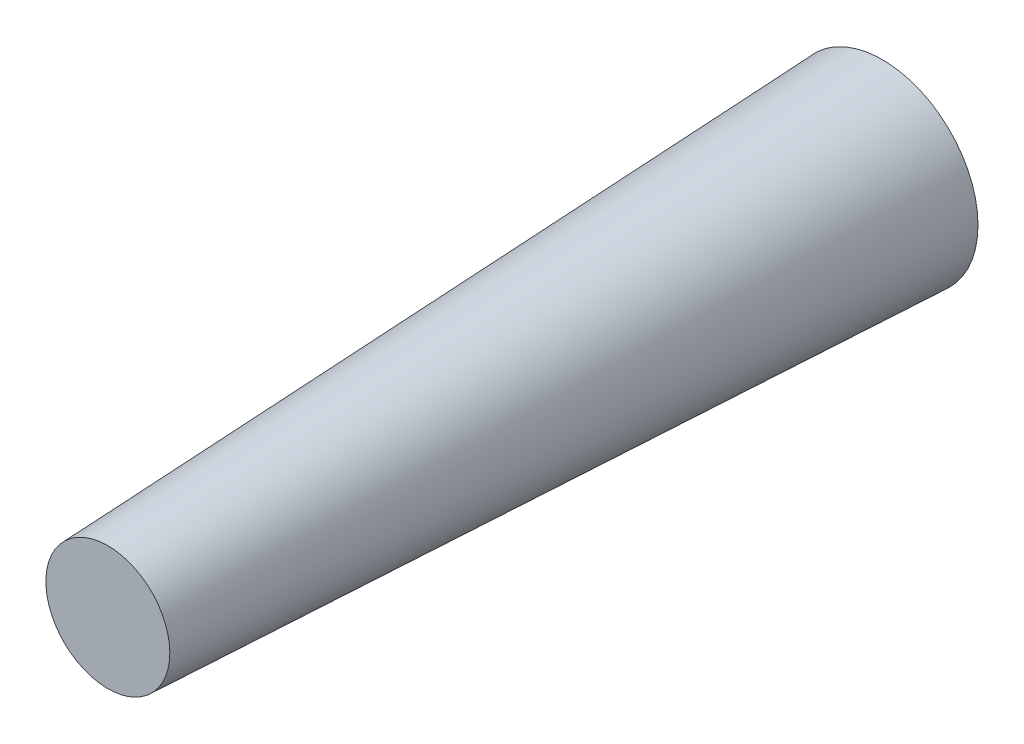
SolidWorks part; units mm, degrees
ref_plane "Front Plane" through (0, 0, 0) normal (0, 0, 1) x (1, 0, 0)
ref_plane "Top Plane" through (0, 0, 0) normal (0, 1, 0) x (1, 0, 0)
ref_plane "Right Plane" through (0, 0, 0) normal (1, 0, 0) x (0, 0, -1)
sketch "Sketch1" plane through (0, 0, 0) normal (0, 0, 1) x (1, 0, 0)
  circle A0 centre (0, 0) radius 18.5
ref_plane "Plane1" through (0, 0, 150) normal (0, 0, 1) x (1, 0, 0)
sketch "Sketch2" plane through (0, 0, 150) normal (0, 0, 1) x (1, 0, 0)
  circle A0 centre (0, 0) radius 12
loft "Loft1" add profiles "Sketch1", "Sketch2"
